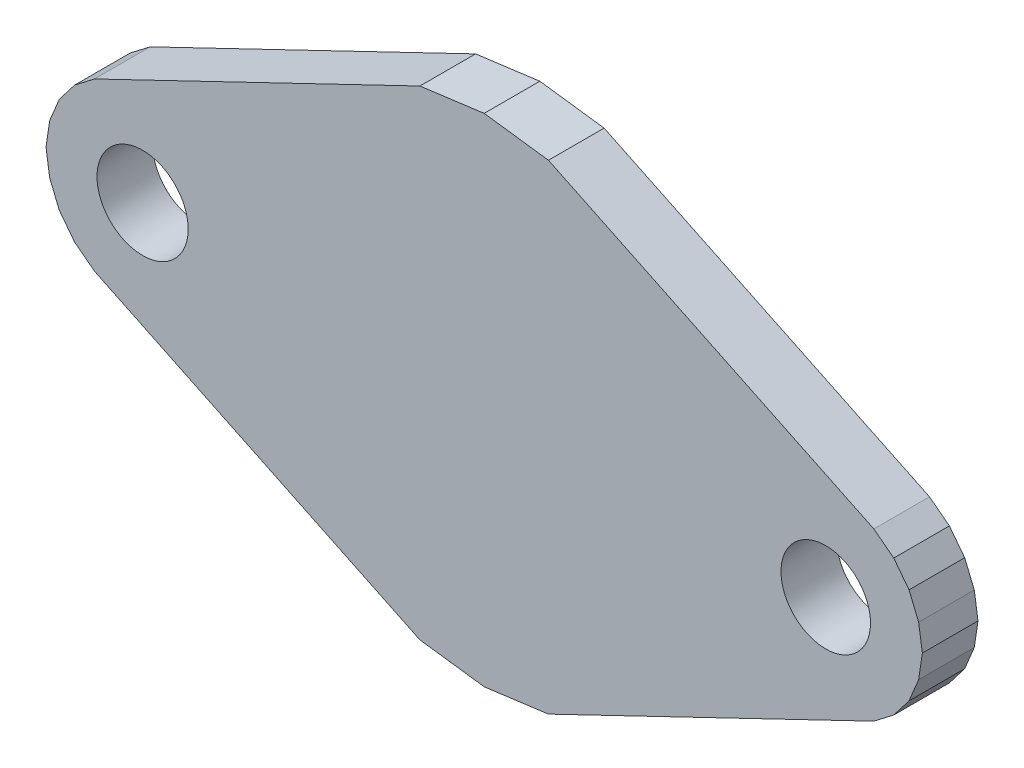
SolidWorks part; units mm, degrees
ref_plane "Plano frontal" through (0, 0, 0) normal (0, 0, 1) x (1, 0, 0)
ref_plane "Plano superior" through (0, 0, 0) normal (0, 1, 0) x (1, 0, 0)
ref_plane "Plano direito" through (0, 0, 0) normal (1, 0, 0) x (0, 0, -1)
other "Gráfico1"
other "Gráfico (Fechado) -1"
sketch "Esboço1" plane through (0, 0, 0) normal (0, 0, 1) x (1, 0, 0)
  line L0 (-3.4409, 5.1642) -> (-20.9829, -3.2768)
  line L1 (-20.9829, -3.2768) -> (-22.0564, -4.1005)
  line L2 (-22.0564, -4.1005) -> (-22.8801, -5.1739)
  line L3 (-22.8801, -5.1739) -> (-23.3979, -6.424)
  line L4 (-23.3979, -6.424) -> (-23.5984, -7.7655)
  line L5 (-23.5984, -7.7655) -> (-23.3979, -9.107)
  line L6 (-23.3979, -9.107) -> (-22.8801, -10.357)
  line L7 (-22.0564, -11.4305) -> (-20.9829, -12.2542)
  line L8 (-22.0564, -11.4305) -> (-22.8801, -10.357)
  line L9 (-20.9829, -12.2542) -> (-3.4409, -20.6952)
  line L10 (-3.4409, -20.6952) -> (0.0236, -21.1513)
  line L11 (0.0236, -21.1513) -> (3.4881, -20.6952)
  line L12 (0.0236, 5.6203) -> (0.0236, -21.1513)
  line L13 (0.0236, -21.1513) -> (-3.4409, -20.6952)
  line L14 (3.4881, -20.6952) -> (0.0236, -21.1513)
  line L15 (21.0302, -12.2542) -> (3.4881, -20.6952)
  line L16 (22.1036, -11.4305) -> (22.9273, -10.357)
  line L17 (22.1036, -11.4305) -> (21.0302, -12.2542)
  line L18 (23.4451, -9.107) -> (22.9273, -10.357)
  line L19 (23.6456, -7.7655) -> (23.4451, -9.107)
  line L20 (23.4451, -6.424) -> (23.6456, -7.7655)
  line L21 (22.9273, -5.1739) -> (23.4451, -6.424)
  line L22 (22.1036, -4.1005) -> (22.9273, -5.1739)
  line L23 (21.0302, -3.2768) -> (22.1036, -4.1005)
  line L24 (3.4881, 5.1642) -> (21.0302, -3.2768)
  line L25 (-3.4409, 5.1642) -> (0.0236, 5.6203)
  line L26 (0.0236, 5.6203) -> (3.4881, 5.1642)
  circle A0 centre (-18.3914, -7.7655) radius 2.4583
  circle A1 centre (18.4386, -7.7655) radius 2.413
extrude "Ressalto-extrusão2" add sketch "Esboço1" along normal blind 3 contours L25 L0 L1 L2 L3 L4 L5 L6 L8 L7 L9 L10 L12 A0 | L26 L12 L11 L15 L17 L16 L18 L19 L20 L21 L22 L23 L24 A1
